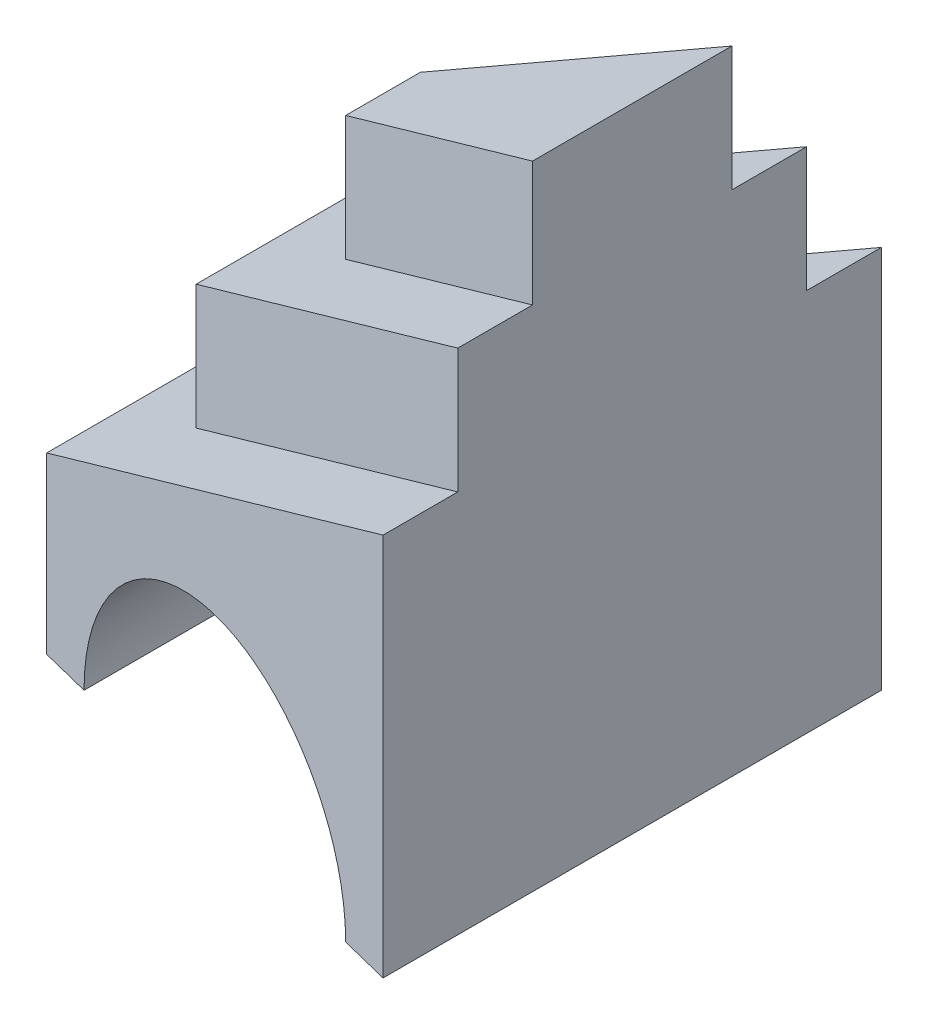
SolidWorks part; units mm, degrees
other "Perspective"
ref_plane "Front Plane" through (0, 0, 0) normal (0, 0, 1) x (1, 0, 0)
ref_plane "Top Plane" through (0, 0, 0) normal (0, 1, 0) x (1, 0, 0)
ref_plane "Right Plane" through (0, 0, 0) normal (1, 0, 0) x (0, 0, -1)
sketch "Sketch1" plane through (0, 0, 0) normal (0, 1, 0) x (1, 0, 0)
  line L0 (0, 0) -> (0, 55)
  line L1 (0, 55) -> (90, 77.5)
  line L2 (90, 77.5) -> (90, -22.5)
  line L3 (90, -22.5) -> (0, 0)
  line L4 (0, 27.5) -> (90, 27.5) construction
  line L5 (167.9905, -22.5) -> (257.9905, -22.5) construction
  line L6 (257.9905, -22.5) -> (257.9905, 54.4677) construction
  line L7 (257.9905, 54.4677) -> (167.9905, 12.5) construction
  line L8 (167.9905, 12.5) -> (167.9905, -22.5) construction
  line L9 (257.9905, 54.4677) -> (167.9905, 54.4677) construction
  line L10 (167.9905, 54.4677) -> (167.9905, 12.5) construction
  dimension "D1" = 100
  dimension "D2" = 55
  dimension "D3" = 90
  dimension "D4" = 90
  dimension "D5" = 25
  dimension "D6" = 35
  dimension "D7" = 76.9677
extrude "Extrude1" add sketch "Sketch1" along normal blind 76.968
sketch "Sketch2" plane through (0, 0, 0) normal (0, 0, 1) x (1, 0, 0)
  line L0 (90, 76.968) -> (0, 35.0003)
  line L1 (0, 76.968) -> (0, 0) construction
  line L2 (0, 35.0003) -> (0, 76.968)
  line L3 (0, 76.968) -> (90, 76.968)
  dimension "D1" = 25
extrude "Extrude2" cut sketch "Sketch2" against normal mid plane 180
sketch "Sketch3" plane through (0, 0, 0) normal (0, 1, 0) x (1, 0, 0)
  line L0 (90, 62.5) -> (20, 45)
  line L1 (90, -22.5) -> (90, 77.5) construction
  line L2 (20, 45) -> (20, 10)
  line L3 (20, 10) -> (90, -7.5)
  line L4 (90, -7.5) -> (90, 62.5)
  line L5 (0, 55) -> (90, 77.5) construction
  line L6 (90, -22.5) -> (0, 0) construction
  line L7 (20, 27.5) -> (90, 27.5) construction
  line L8 (0, 55) -> (0, 0) construction
  line L9 (143.1743, -7.5) -> (233.1743, -7.5) construction
  line L10 (233.1743, -7.5) -> (233.1743, 94.4677) construction
  line L11 (233.1743, 94.4677) -> (143.1743, 52.5) construction
  line L12 (143.1743, 52.5) -> (143.1743, -7.5) construction
  line L13 (233.1743, 94.4677) -> (143.1743, 94.4677) construction
  line L14 (143.1743, 94.4677) -> (143.1743, 52.5) construction
  dimension "D1" = 35
  dimension "D2" = 25
  dimension "D3" = 20
  dimension "D4" = 60
  dimension "D5" = 90
  dimension "D6" = 101.9677
extrude "Extrude3" add sketch "Sketch3" along normal blind 101.968
sketch "Sketch4" plane through (0, 0, 0) normal (0, 0, 1) x (1, 0, 0)
  line L0 (90, 101.968) -> (20, 69.3265)
  line L1 (20, 101.968) -> (20, 44.3265) construction
  line L2 (20, 69.3265) -> (20, 101.968)
  line L3 (20, 101.968) -> (90, 101.968)
  line L4 (90, 76.968) -> (0, 35.0003) construction
extrude "Extrude4" cut sketch "Sketch4" against normal mid plane 152.642
sketch "Sketch5" plane through (0, 0, 0) normal (0, 1, 0) x (1, 0, 0)
  line L0 (90, 47.5) -> (40, 35)
  line L1 (90, -7.5) -> (90, 62.5) construction
  line L2 (40, 35) -> (40, 20)
  line L3 (40, 20) -> (90, 7.5)
  line L4 (40, 27.5) -> (90, 27.5) construction
  line L5 (20, 45) -> (20, 10) construction
  line L6 (90, 47.5) -> (90, 7.5)
  line L7 (20, 45) -> (90, 62.5) construction
  line L8 (90, -7.5) -> (20, 10) construction
  line L9 (152.1659, 7.5) -> (242.1659, 7.5) construction
  line L10 (242.1659, 7.5) -> (242.1659, 134.4677) construction
  line L11 (242.1659, 134.4677) -> (152.1659, 92.5) construction
  line L12 (152.1659, 92.5) -> (152.1659, 7.5) construction
  line L13 (242.1659, 134.4677) -> (152.1659, 134.4677) construction
  line L14 (152.1659, 134.4677) -> (152.1659, 92.5) construction
  dimension "D1" = 15
  dimension "D2" = 20
  dimension "D3" = 25
  dimension "D4" = 90
  dimension "D5" = 85
  dimension "D6" = 126.9677
extrude "Extrude5" add sketch "Sketch5" along normal blind 126.968
sketch "Sketch6" plane through (0, 0, 0) normal (0, 0, 1) x (1, 0, 0)
  line L0 (90, 126.968) -> (40, 103.6526)
  line L1 (40, 126.968) -> (40, 78.6526) construction
  line L2 (40, 103.6526) -> (40, 126.968)
  line L3 (40, 126.968) -> (90, 126.968)
  line L5 (90, 101.968) -> (20, 69.3265) construction
extrude "Extrude6" cut sketch "Sketch6" against normal blind 126.968
sketch "Sketch7" plane through (0, 0, 0) normal (0, 0, 1) x (1, 0, 0)
  line L0 (0, 0) -> (90, 0) construction
  line L1 (80, 0) -> (10, 0)
  arc A0 (80, 0) -> (10, 0) centre (45, 0) ccw
  dimension "D1" = 10
extrude "Extrude7" cut sketch "Sketch7" against normal mid plane 176.968
